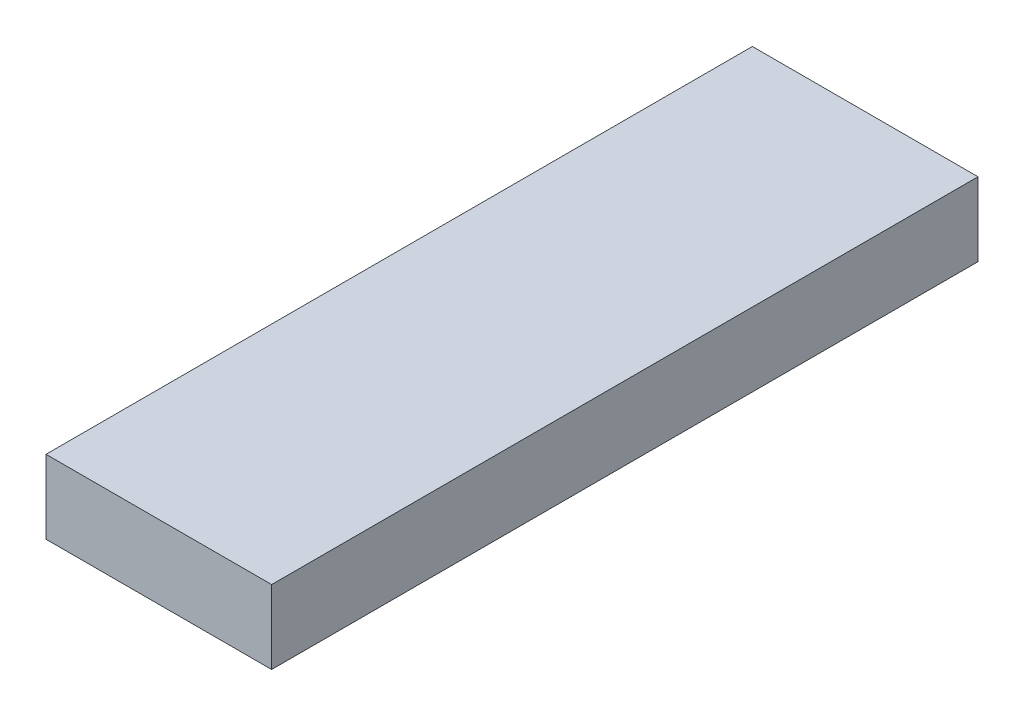
SolidWorks part; units mm, degrees
ref_plane "Front Plane" through (0, 0, 0) normal (0, 0, 1) x (1, 0, 0)
ref_plane "Top Plane" through (0, 0, 0) normal (0, 1, 0) x (1, 0, 0)
ref_plane "Right Plane" through (0, 0, 0) normal (1, 0, 0) x (0, 0, -1)
sketch "Sketch1" plane through (0, 0, 0) normal (0, 1, 0) x (1, 0, 0)
  line L2 (-23, 72) -> (23, 72)
  line L5 (-19, 72) -> (-19, 90)
  line L6 (-19, 90) -> (-4, 90)
  line L7 (-4, 90) -> (-4, 72)
  line L8 (4, 72) -> (4, 90)
  line L9 (4, 90) -> (19, 90)
  line L10 (19, 90) -> (19, 72)
  line L11 (0, 72) -> (0, 180.6197) construction
  line L13 (23, -72) -> (-23, -72)
  line L14 (23, -72) -> (23, 72)
  line L16 (-23, -72) -> (-23, 72)
  line L17 (23, -72) -> (-23, 72) construction
  line L18 (23, 72) -> (-23, -72) construction
  point P0 (0, 0)
  point P1 (23, 142.2673)
  point P16 (-11.5, 90)
  point P17 (11.5, 90)
  point P20 (-23, 142.2268)
  dimension "D1" = 144
  dimension "D2" = 46
  dimension "D3" = 15
  dimension "D4" = 23
  dimension "D5" = 18
extrude "Boss-Extrude1" add sketch "Sketch1" along normal blind 15 contours L2 L14 L13 L16
